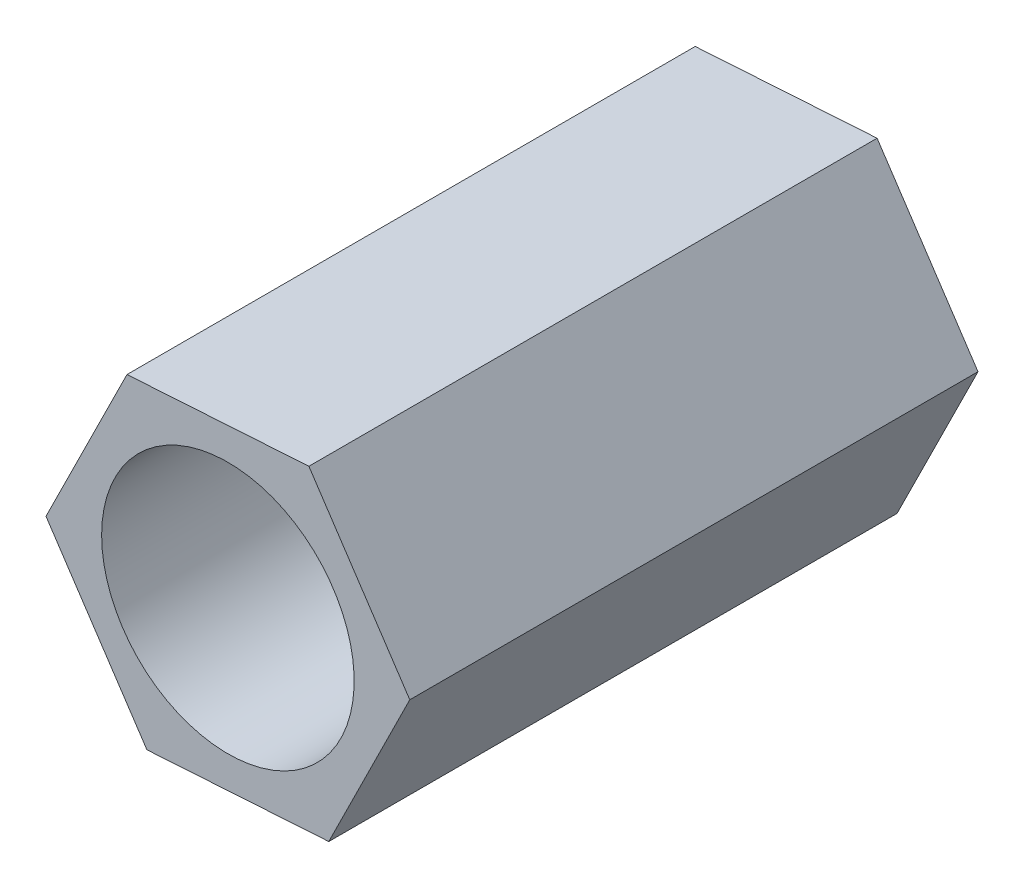
SolidWorks part; units mm, degrees
ref_plane "前视基准面" through (0, 0, 0) normal (0, 0, 1) x (1, 0, 0)
ref_plane "上视基准面" through (0, 0, 0) normal (0, 1, 0) x (1, 0, 0)
ref_plane "右视基准面" through (0, 0, 0) normal (1, 0, 0) x (0, 0, -1)
sketch "草图1" plane through (0, 0, 0) normal (0, 0, 1) x (1, 0, 0)
  line L1 (1.2828, 2.586) -> (-1.5982, 2.404)
  line L2 (-1.5982, 2.404) -> (-2.881, -0.182)
  line L3 (-2.881, -0.182) -> (-1.2828, -2.586)
  line L4 (-1.2828, -2.586) -> (1.5982, -2.404)
  line L5 (1.5982, -2.404) -> (2.881, 0.182)
  line L6 (2.881, 0.182) -> (1.2828, 2.586)
  circle A0 centre (0, 0) radius 2.5 construction
  dimension "D1" = 5
extrude "凸台-拉伸1" add sketch "草图1" along normal blind 9
sketch "草图2" plane through (0, 0, 0) normal (0, 0, -1) x (-1, 0, 0)
  circle A0 centre (0, 0) radius 2
  dimension "D1" = 4
extrude "切除-拉伸1" cut sketch "草图2" against normal through all
